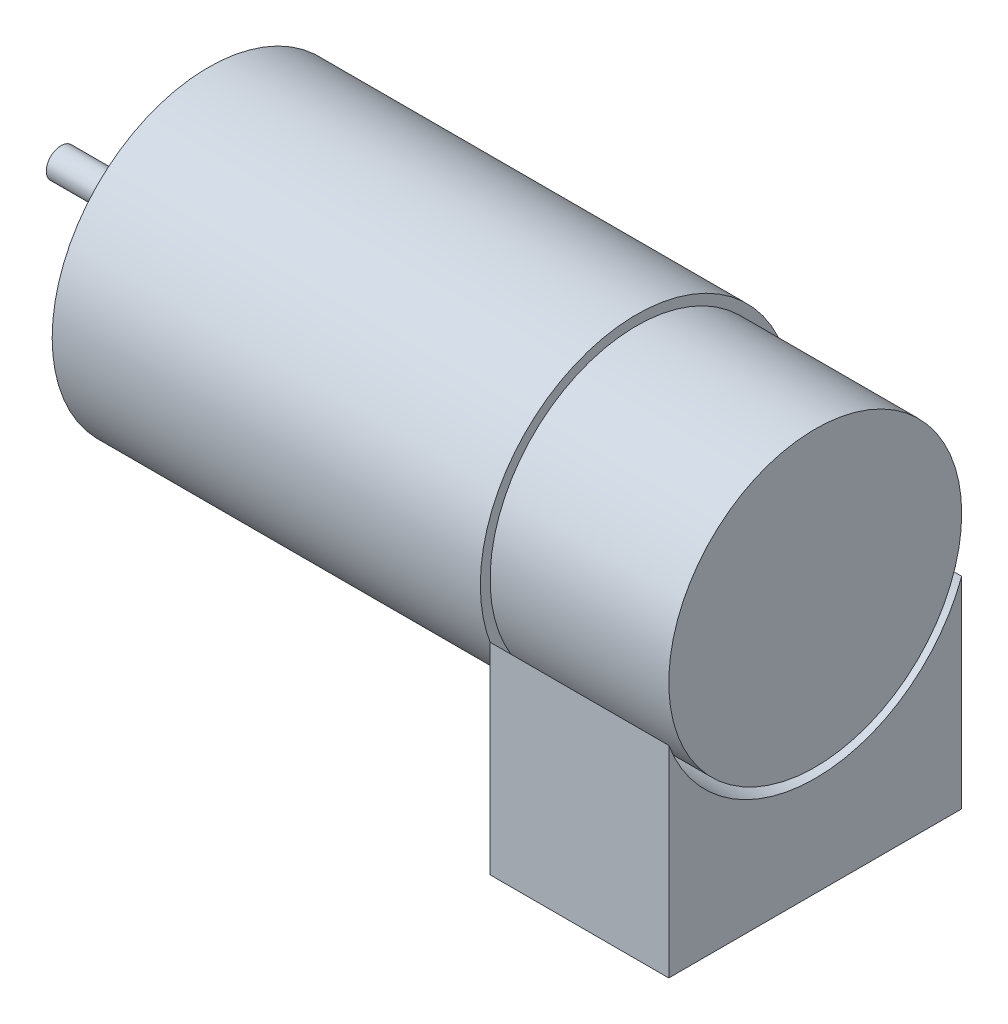
SolidWorks part; units mm, degrees
ref_plane "Front" through (0, 0, 0) normal (0, 0, 1) x (1, 0, 0)
ref_plane "Top" through (0, 0, 0) normal (0, 1, 0) x (1, 0, 0)
ref_plane "Right" through (0, 0, 0) normal (1, 0, 0) x (0, 0, -1)
sketch "Sketch1" plane through (0, 0, 0) normal (0, 1, 0) x (1, 0, 0)
  line L0 (0, 0) -> (67682.5633, 0) construction
  line L1 (0, 0) -> (0, 1.5)
  line L2 (0, 1.5) -> (13, 1.5)
  line L3 (13, 1.5) -> (13, 0)
  line L4 (13, 0) -> (13, 5)
  line L5 (13, 5) -> (15.1, 5)
  line L6 (15.1, 5) -> (15.1, 0)
  line L7 (15.1, 0) -> (15.1, 16)
  line L8 (15.1, 16) -> (58.95, 16)
  line L9 (58.95, 16) -> (58.95, 0)
  line L10 (0, 0) -> (58.95, 0)
  dimension "D1" = 1.5
  dimension "D2" = 13
  dimension "D3" = 5
  dimension "D4" = 2.1
  dimension "D5" = 16
  dimension "D6" = 43.85
revolve "Revolve3" add sketch "Sketch1" angle 360 about L0
sketch "Sketch2" plane through (58.95, 0, 0) normal (1, 0, 0) x (0, 0, -1)
  line L0 (0, 0) -> (-25.2, 0) construction
  line L1 (0, 0) -> (0, 16.9873) construction
  line L6 (0, 0) -> (-15, 0)
  line L7 (-15, 0) -> (-15, -26.2)
  line L8 (-15, -26.2) -> (15, -26.2)
  line L9 (15, -26.2) -> (15, 0)
  line L10 (15, 0) -> (0, 0)
  circle A0 centre (0, 0) radius 15
  circle M4 centre (0, 0) radius 16
  dimension "D1" = 15
  dimension "D2" = 15
  dimension "D3" = 26.2
extrude "Boss-Extrude1" add sketch "Sketch2" along normal blind 18.3 contours L8 L9 L7 M4 | L6 A0 L10 | L10 A0 L6
sketch "Sketch3" plane through (15.1, 0, 0) normal (-1, 0, 0) x (0, 0, 1)
  line L0 (0, 0) -> (0, 120) construction
  line L1 (0, 0) -> (-13.8564, -8) construction
  line L2 (0, 0) -> (13.8564, -8) construction
  circle A0 centre (0, 0) radius 16 construction
  circle A1 centre (0, 0) radius 8.5
  dimension "D1" = 120
  dimension "D2" = 120
hole_wizard "Tap Drill for M2 Tap1" positions "3DSketch1" profile "Sketch4" hole size "M2" standard "ISO"
sketch3d "3DSketch1"
  line L0 (15.1, 0, 0) -> (15.1, 120, 0) construction
  line L1 (15.1, 0, 0) -> (15.1, -8, 13.8564) construction
  circle A0 centre (15.1, 0, 0) radius 8.5 construction
  point P0 (15.1, 8.5, 0)
  point P4 (6.6, 0, 0)
  point P7 (15.1, -4.2872, -7.3396)
  point P9 (15.1, -4.25, 7.3612)
  point P13 (15.1, -8.4998, 0.0546)
sketch "Sketch4" plane through (15.1, 8.5, 0) normal (0, 1, 0) x (0, 0, 1)
  line L0 (0, 0) -> (0, 3.6)
  line L1 (0, 3.6) -> (0.8, 3.1193)
  line L2 (0.8, 3.1193) -> (0.8, 0)
  line L5 (0.8, 0) -> (0, 0)
  line L10 (0, 3.6) -> (-0.8, 3.1193) construction
  line L11 (0, -6.35) -> (0, 107.95) construction
  dimension "Hole Dia." = 1.6
  dimension "Hole Depth" = 3.6
  dimension "Drill Angle" = 118
